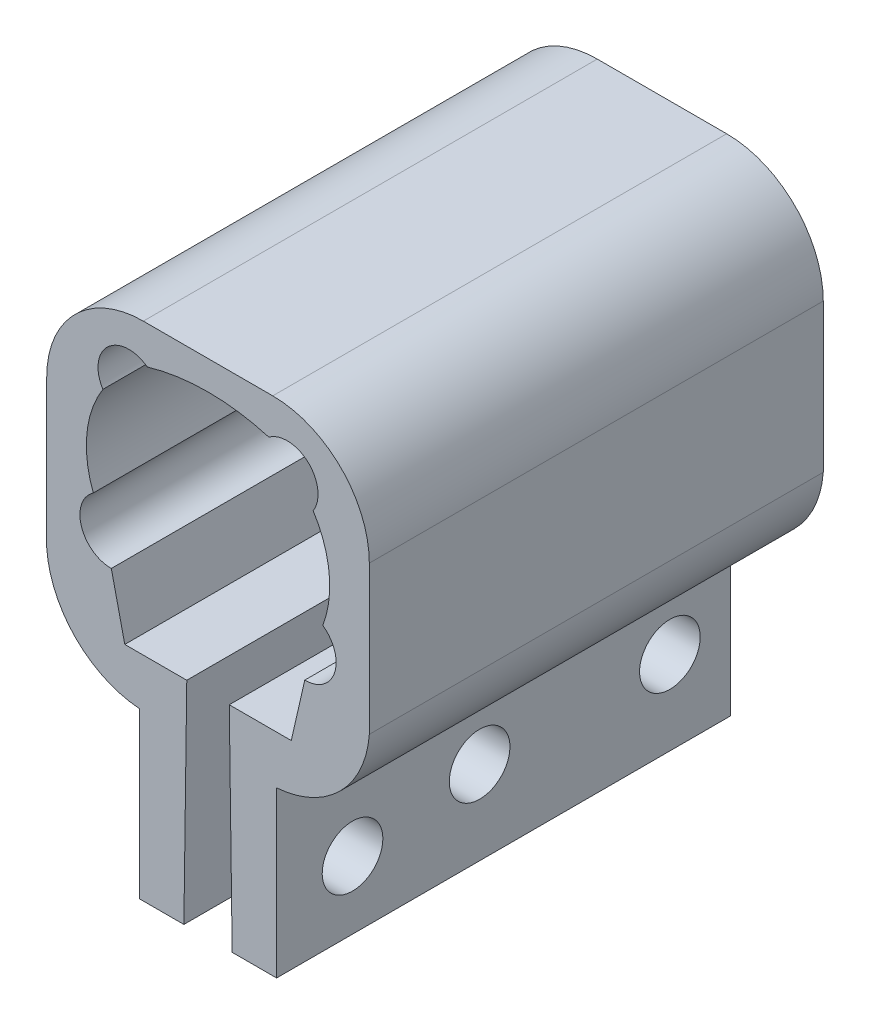
SolidWorks part; units mm, degrees
ref_plane "Front Plane" through (0, 0, 0) normal (0, 0, 1) x (1, 0, 0)
ref_plane "Top Plane" through (0, 0, 0) normal (0, 1, 0) x (1, 0, 0)
ref_plane "Right Plane" through (0, 0, 0) normal (1, 0, 0) x (0, 0, -1)
sketch "Sketch30" plane through (0, 0, -44.196) normal (0, 0, -1) x (-1, 0, 0)
  line L4 (-21.1226, -11.2308) -> (-19.3514, -18.9991)
  line L6 (2.541, -18.9991) -> (4.3123, -11.2308)
  line L8 (-8.4052, 19.0361) -> (-8.4052, 15.2261) construction
  line L9 (-5.2302, -47.0039) -> (0.6118, -47.0039)
  line L10 (12.8038, -13.1571) -> (12.8038, 6.3361) construction
  line L11 (-29.6142, -13.1571) -> (-29.6142, 6.3361) construction
  line L12 (-8.4052, -47.0039) -> (-5.2302, -47.0039) construction
  line L13 (-8.4052, 19.0361) -> (0.1038, 19.0361) construction
  line L14 (-8.4052, 19.0361) -> (-16.9142, 19.0361) construction
  line L15 (12.8038, -13.1571) -> (12.8038, 6.3361)
  line L16 (0.1038, 19.0361) -> (-16.9142, 19.0361)
  line L17 (-29.6142, 6.3361) -> (-29.6142, -13.1571)
  line L19 (12.8038, 6.3361) -> (12.8038, -13.1571) construction
  line L23 (-11.5802, -47.0039) -> (-17.4222, -47.0039)
  line L24 (-8.4052, -47.0039) -> (-11.5802, -47.0039) construction
  line L25 (-5.2302, -47.0039) -> (-5.6112, -18.9991)
  line L26 (-11.5802, -47.0039) -> (-11.1992, -18.9991)
  line L27 (-5.6112, -18.9991) -> (2.541, -18.9991)
  line L28 (-11.1992, -18.9991) -> (-19.3514, -18.9991)
  line L29 (-8.4052, -47.0039) -> (-8.4052, 19.0361) construction
  line L30 (0.6118, -47.0039) -> (0.6118, -26.6839)
  line L31 (-17.4222, -47.0039) -> (-17.4222, -26.6839)
  line L32 (-17.4222, -26.6839) -> (-17.4222, -25.3491)
  line L34 (0.6118, -26.6839) -> (0.6118, -25.3491) construction
  line L35 (0.6118, -25.3491) -> (0.6118, -26.6839)
  arc A6 (4.3123, -11.2308) -> (6.6793, -3.8197) centre (4.375, -7.1673) ccw
  arc A7 (6.6793, -3.8197) -> (5.4174, 8.6125) centre (-6.2889, 1.1441) ccw
  arc A8 (5.4174, 8.6125) -> (-0.4159, 14.0791) centre (1.9989, 10.8103) ccw
  arc A9 (-22.2277, 8.6125) -> (-16.3944, 14.0791) centre (-18.8093, 10.8103) cw
  arc A10 (-23.4896, -3.8197) -> (-22.2277, 8.6125) centre (-10.5214, 1.1441) cw
  arc A11 (-21.1226, -11.2308) -> (-23.4896, -3.8197) centre (-21.1854, -7.1673) cw
  arc A12 (-0.4159, 14.0791) -> (-16.3944, 14.0791) centre (-8.4052, -13.1716) ccw
  arc A13 (-29.6142, 6.3361) -> (-16.9142, 19.0361) centre (-16.9142, 6.3361) cw
  arc A14 (0.1038, 19.0361) -> (12.8038, 6.3361) centre (0.1038, 6.3361) cw
  arc A15 (12.8038, -13.1571) -> (0.6118, -25.3491) centre (-0.3513, -12.194) cw
  arc A16 (-29.6142, -13.1571) -> (-17.4222, -25.3491) centre (-16.459, -12.194) ccw
extrude "Boss-Extrude1" add sketch "Sketch30" along normal blind 59.69
sketch "Sketch31" plane through (17.4222, 0, 0) normal (1, 0, 0) x (0, 0, -1)
  line L0 (103.886, -47.0039) -> (95.9104, -47.0039) construction
  line L1 (103.886, -47.0039) -> (44.196, -47.0039) construction
  line L2 (95.9104, -47.0039) -> (95.9104, -36.0057) construction
  line L3 (103.886, -47.0039) -> (70.8914, -47.0039) construction
  line L4 (70.8914, -47.0039) -> (70.8914, -36.0057) construction
  line L5 (44.196, -47.0039) -> (54.1782, -47.0039) construction
  line L6 (54.1782, -47.0039) -> (54.1782, -38.1139) construction
  circle A0 centre (95.9104, -36.0057) radius 3.9878
  circle A1 centre (70.8914, -36.0057) radius 3.9878
  circle A2 centre (54.1782, -38.1139) radius 3.9878
extrude "Cut-Extrude1" cut sketch "Sketch31" against normal through all
equation "\"Stroke\"= 2"
